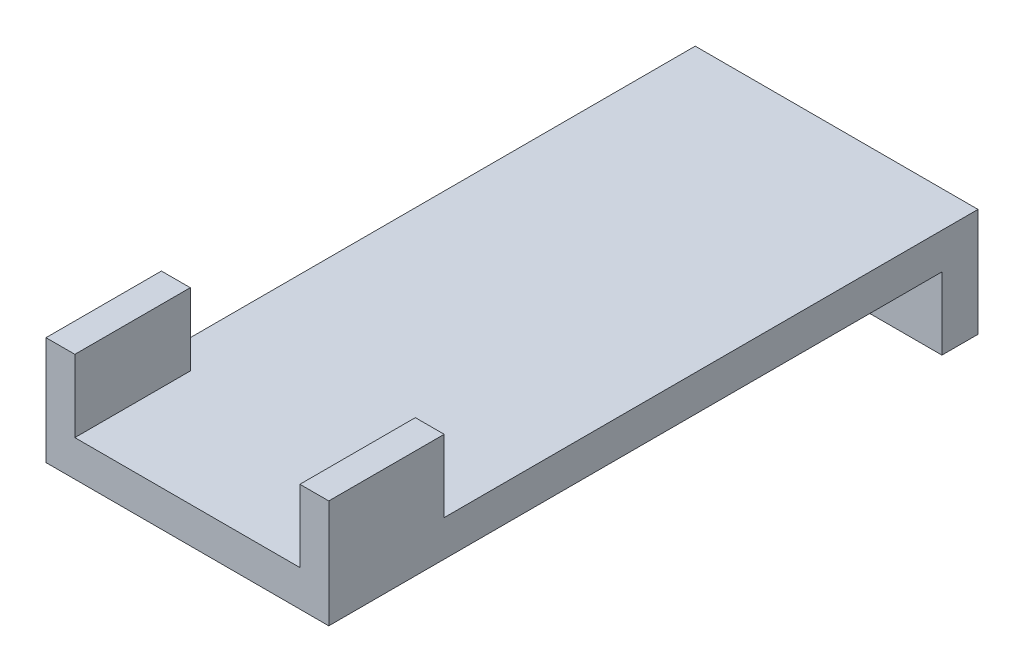
SolidWorks part; units mm, degrees
material "ABS"
ref_plane "Front Plane" through (0, 0, 0) normal (0, 0, 1) x (1, 0, 0)
ref_plane "Top Plane" through (0, 0, 0) normal (0, 1, 0) x (1, 0, 0)
ref_plane "Right Plane" through (0, 0, 0) normal (1, 0, 0) x (0, 0, -1)
sketch "Sketch2" plane through (0, 0, 0) normal (0, 1, 0) x (1, 0, 0)
  line L1 (-12.446, -28.575) -> (12.446, -28.575)
  line L2 (-12.446, -28.575) -> (-12.446, 28.575)
  line L3 (-12.446, 28.575) -> (12.446, 28.575)
  line L4 (12.446, -28.575) -> (12.446, 28.575)
  line L5 (-12.446, -28.575) -> (12.446, 28.575) construction
  line L6 (-12.446, 28.575) -> (12.446, -28.575) construction
  point P0 (0, 0)
  dimension "D1" = 57.15
  dimension "D2" = 24.892
extrude "Boss-Extrude1" add sketch "Sketch2" along normal blind 3.175
sketch "Sketch3" plane through (0, 3.175, 0) normal (0, 1, 0) x (1, 0, 0)
  line L1 (12.446, -28.575) -> (9.906, -28.575)
  line L2 (12.446, -28.575) -> (12.446, -18.415)
  line L3 (12.446, -18.415) -> (9.906, -18.415)
  line L4 (9.906, -28.575) -> (9.906, -18.415)
  line L5 (-12.446, -28.575) -> (-9.906, -28.575)
  line L6 (-12.446, -28.575) -> (-12.446, -18.415)
  line L7 (-12.446, -18.415) -> (-9.906, -18.415)
  line L8 (-9.906, -28.575) -> (-9.906, -18.415)
  dimension "D1" = 2.54
  dimension "D2" = 2.54
  dimension "D3" = 10.16
  dimension "D4" = 10.16
extrude "Boss-Extrude2" add sketch "Sketch3" along normal blind 6.35
sketch "Sketch4" plane through (0, 0, 0) normal (0, -1, 0) x (1, 0, 0)
  line L0 (-12.446, -28.575) -> (-12.446, 28.575) construction
  line L1 (12.446, -28.575) -> (-12.446, -28.575)
  line L2 (12.446, -28.575) -> (12.446, -25.4)
  line L3 (12.446, -25.4) -> (-12.446, -25.4)
  line L4 (-12.446, -28.575) -> (-12.446, -25.4)
  dimension "D1" = 3.175
extrude "Boss-Extrude3" add sketch "Sketch4" along normal blind 6.35
scale "Scale1" scale about centroid uniform scaling yes scale factor 1.02
